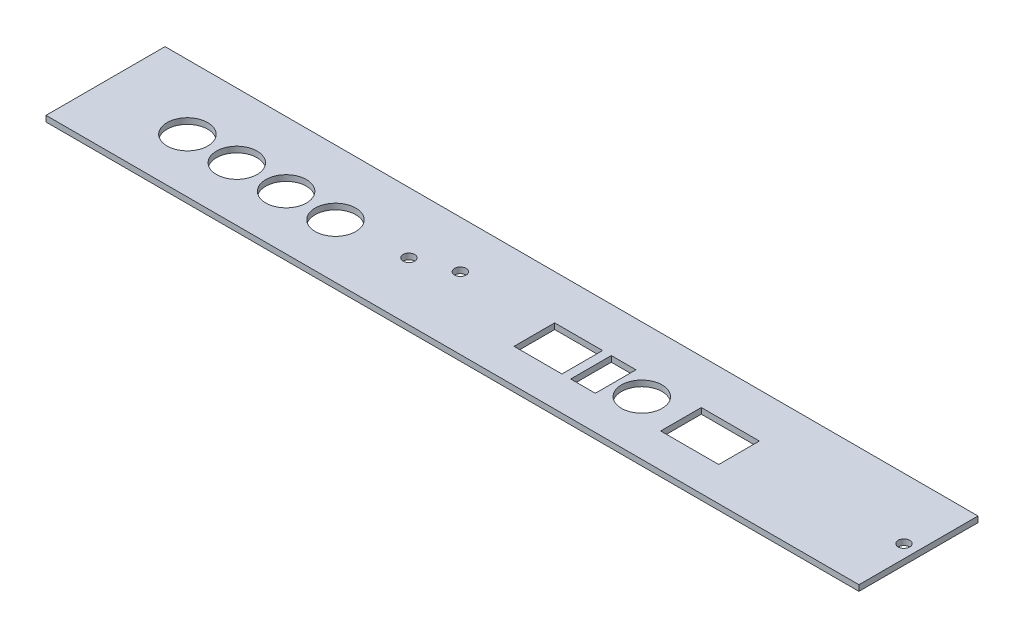
SolidWorks part; units mm, degrees
ref_plane "前视基准面" through (0, 0, 0) normal (0, 0, 1) x (1, 0, 0)
ref_plane "上视基准面" through (0, 0, 0) normal (0, 1, 0) x (1, 0, 0)
ref_plane "右视基准面" through (0, 0, 0) normal (1, 0, 0) x (0, 0, -1)
sketch "草图1" plane through (0, 0, 0) normal (0, 1, 0) x (1, 0, 0)
  line L1 (0, 0) -> (280, 0)
  line L2 (0, 0) -> (0, 41)
  line L3 (0, 41) -> (280, 41)
  line L4 (280, 0) -> (280, 41)
  line L5 (149.5, 11.7) -> (166, 11.7)
  line L6 (149.5, 11.7) -> (149.5, 25.7)
  line L7 (149.5, 25.7) -> (166, 25.7)
  line L8 (166, 11.7) -> (166, 25.7)
  line L9 (169, 11.7) -> (177.5, 11.7)
  line L10 (169, 11.7) -> (169, 25.7)
  line L11 (169, 25.7) -> (177.5, 25.7)
  line L12 (177.5, 11.7) -> (177.5, 25.7)
  line L13 (200, 11.7) -> (220, 11.7)
  line L14 (200, 11.7) -> (200, 25.7)
  line L15 (200, 25.7) -> (220, 25.7)
  line L16 (220, 11.7) -> (220, 25.7)
  circle A0 centre (30, 18.7) radius 7
  circle A1 centre (47, 18.7) radius 7
  circle A2 centre (64, 18.7) radius 7
  circle A3 centre (81, 18.7) radius 7
  circle A4 centre (186.5, 18.7) radius 7
  circle A5 centre (118, 24.7) radius 2
  circle A6 centre (105, 20) radius 2
  circle A7 centre (275.5, 20) radius 2
  dimension "D1" = 4
extrude "凸台-拉伸1" add sketch "草图1" along normal blind 2
